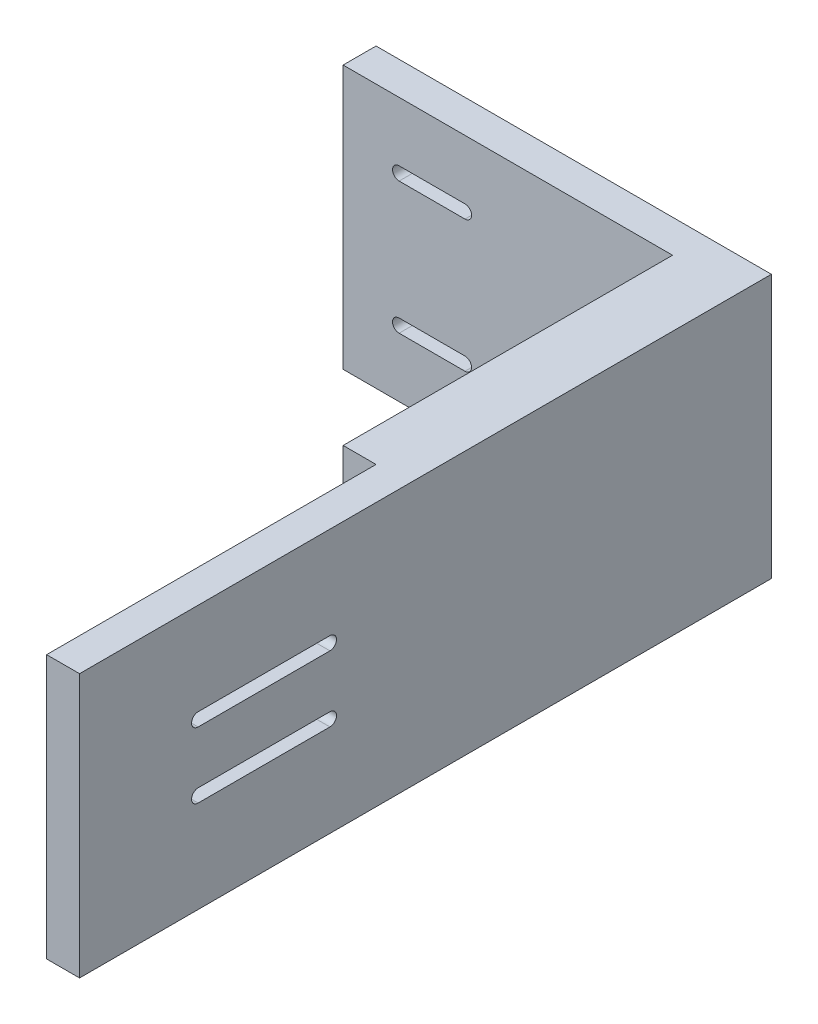
SolidWorks part; units mm, degrees
ref_plane "前视基准面" through (0, 0, 0) normal (0, 0, 1) x (1, 0, 0)
ref_plane "上视基准面" through (0, 0, 0) normal (0, 1, 0) x (1, 0, 0)
ref_plane "右视基准面" through (0, 0, 0) normal (1, 0, 0) x (0, 0, -1)
sketch "草图1" plane through (0, 0, 0) normal (0, 0, 1) x (1, 0, 0)
  line L1 (-30, 20) -> (30, 20)
  line L2 (-30, 20) -> (-30, -20)
  line L3 (-30, -20) -> (30, -20)
  line L4 (30, 20) -> (30, -20)
  line L5 (-30, 20) -> (30, -20) construction
  line L6 (-30, -20) -> (30, 20) construction
  point P0 (0, 0)
  dimension "D1" = 60
  dimension "D2" = 40
extrude "凸台-拉伸1" add sketch "草图1" along normal blind 5
sketch "草图2" plane through (0, 0, 5) normal (0, 0, 1) x (1, 0, 0)
  line L0 (30, 20) -> (-30, 20) construction
  line L1 (20, 20) -> (30, 20)
  line L2 (20, 20) -> (20, -20)
  line L3 (20, -20) -> (30, -20)
  line L4 (30, 20) -> (30, -20)
  dimension "D1" = 10
extrude "凸台-拉伸2" add sketch "草图2" along normal blind 100
sketch "草图3" plane through (20, 0, 0) normal (-1, 0, 0) x (0, 0, 1)
  line L0 (5, 20) -> (5, -20) construction
  line L1 (5, 0) -> (90.5048, 0) construction
  circle A0 centre (30, 0) radius 1
  point P6 (0, 0)
  dimension "D1" = 2
  dimension "D2" = 25
extrude "凸台-拉伸3" add sketch "草图3" along normal blind 2.5
sketch "草图4" plane through (20, 0, 0) normal (-1, 0, 0) x (0, 0, 1)
  line L0 (67, 5) -> (87, 5) construction
  line L1 (67, 6) -> (87, 6)
  line L2 (67, 4) -> (87, 4)
  line L3 (0, 0) -> (37.6183, 0) construction
  line L4 (67, -5) -> (87, -5) construction
  line L5 (67, -6) -> (87, -6)
  line L6 (67, -4) -> (87, -4)
  arc A0 (67, 6) -> (67, 4) centre (67, 5) ccw
  arc A1 (87, 4) -> (87, 6) centre (87, 5) ccw
  arc A2 (67, -6) -> (67, -4) centre (67, -5) cw
  arc A3 (87, -4) -> (87, -6) centre (87, -5) cw
  circle A4 centre (30, 0) radius 1 construction
  point P2 (77, 5)
  point P12 (77, -5)
  dimension "D1" = 1
  dimension "D2" = 5
  dimension "D3" = 37
  dimension "D4" = 20
extrude "切除-拉伸1" cut sketch "草图4" against normal through all
sketch "草图5" plane through (0, -20, 0) normal (0, -1, 0) x (1, 0, 0)
  line L1 (20, 105) -> (25, 105)
  line L2 (20, 105) -> (20, 55)
  line L3 (20, 55) -> (25, 55)
  line L4 (25, 105) -> (25, 55)
  dimension "D1" = 5
  dimension "D2" = 50
extrude "切除-拉伸2" cut sketch "草图5" against normal through all
sketch "草图6" plane through (0, 0, 5) normal (0, 0, 1) x (1, 0, 0)
  line L1 (0, 0) -> (49.9721, 0) construction
  line L2 (-11.5, 10) -> (-21.5, 10) construction
  line L3 (-11.5, 9.0015) -> (-21.5, 9.0015)
  line L4 (-11.5, 10.9985) -> (-21.5, 10.9985)
  line L5 (-11.5, -10) -> (-21.5, -10) construction
  line L6 (-11.5, -9.0015) -> (-21.5, -9.0015)
  line L7 (-11.5, -10.9985) -> (-21.5, -10.9985)
  line L8 (30, -20) -> (30, 20) construction
  arc A2 (-11.5, 9.0015) -> (-11.5, 10.9985) centre (-11.5, 10) ccw
  arc A3 (-21.5, 10.9985) -> (-21.5, 9.0015) centre (-21.5, 10) ccw
  arc A4 (-11.5, -9.0015) -> (-11.5, -10.9985) centre (-11.5, -10) cw
  arc A5 (-21.5, -10.9985) -> (-21.5, -9.0015) centre (-21.5, -10) cw
  point P1 (0, 0)
  point P9 (-16.5, 10)
  point P16 (-16.5, -10)
  dimension "D2" = 10
  dimension "D4" = 1.9971
  dimension "D1" = 41.5
  dimension "D5" = 10
extrude "切除-拉伸3" cut sketch "草图6" against normal up to next
